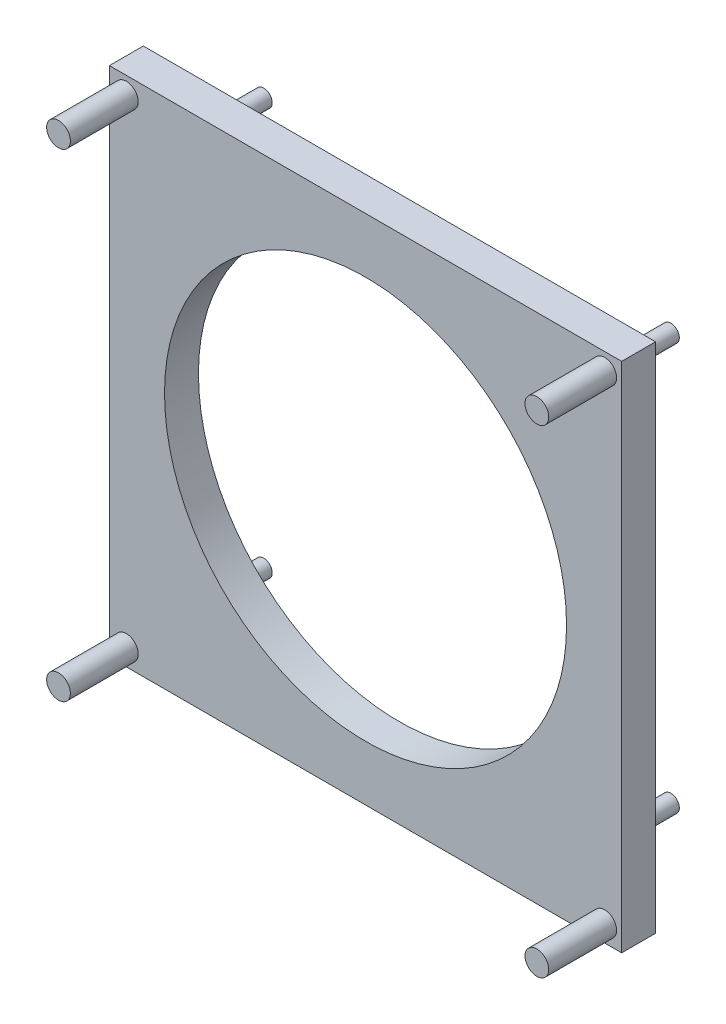
SolidWorks part; units mm, degrees
ref_plane "Front Plane" through (0, 0, 0) normal (0, 0, 1) x (1, 0, 0)
ref_plane "Top Plane" through (0, 0, 0) normal (0, 1, 0) x (1, 0, 0)
ref_plane "Right Plane" through (0, 0, 0) normal (1, 0, 0) x (0, 0, -1)
sketch "Sketch1" plane through (0, 0, 0) normal (0, 0, 1) x (1, 0, 0)
  line L1 (-225.7582, 128.2518) -> (-74.7582, 128.2518)
  line L2 (-225.7582, 128.2518) -> (-225.7582, -22.7482)
  line L3 (-225.7582, -22.7482) -> (-74.7582, -22.7482)
  line L4 (-74.7582, 128.2518) -> (-74.7582, -22.7482)
  line L5 (-225.7582, 128.2518) -> (-74.7582, -22.7482) construction
  line L6 (-225.7582, -22.7482) -> (-74.7582, 128.2518) construction
  point P0 (-150.2582, 52.7518)
  dimension "D1" = 151
  dimension "D2" = 151
extrude "Boss-Extrude1" add sketch "Sketch1" along normal blind 10
sketch "Sketch3" plane through (0, 0, 10) normal (0, 0, 1) x (1, 0, 0)
  line L0 (-150.2582, 128.2518) -> (-150.2582, -22.7482) construction
  line L1 (-74.7582, 128.2518) -> (-225.7582, 128.2518) construction
  line L2 (-225.7582, -22.7482) -> (-74.7582, -22.7482) construction
  line L3 (-74.7582, 52.7518) -> (-225.7582, 52.7518) construction
  line L4 (-74.7582, -22.7482) -> (-74.7582, 128.2518) construction
  line L5 (-225.7582, 128.2518) -> (-225.7582, -22.7482) construction
  circle A0 centre (-150.2582, 52.7518) radius 59.25
  dimension "D1" = 118.5
extrude "Cut-Extrude1" cut sketch "Sketch3" against normal through all
sketch "Sketch4" plane through (0, 0, 10) normal (0, 0, 1) x (1, 0, 0)
  line L0 (-220.7582, 128.2518) -> (-220.7582, -22.7482) construction
  line L1 (-74.7582, 128.2518) -> (-225.7582, 128.2518) construction
  line L2 (-225.7582, -22.7482) -> (-74.7582, -22.7482) construction
  line L3 (-225.7582, -17.7482) -> (-74.7582, -17.7482) construction
  line L4 (-225.7582, 128.2518) -> (-225.7582, -22.7482) construction
  line L5 (-74.7582, -22.7482) -> (-74.7582, 128.2518) construction
  line L6 (-79.7582, -22.7482) -> (-79.7582, 128.2518) construction
  line L7 (-225.7582, 123.2518) -> (-74.7582, 123.2518) construction
  circle A0 centre (-79.7582, -17.7482) radius 3.5
  circle A1 centre (-220.7582, -17.7482) radius 3.5
  circle A2 centre (-79.7582, 123.2518) radius 3.5
  circle A3 centre (-220.7582, 123.2518) radius 3.5
  dimension "D1" = 5
  dimension "D2" = 5
  dimension "D3" = 5
  dimension "D4" = 5
extrude "Boss-Extrude2" add sketch "Sketch4" along normal blind 20
sketch "Sketch5" plane through (0, 0, 0) normal (0, 0, -1) x (-1, 0, 0)
  line L0 (74.7582, -7.2482) -> (225.7582, -7.2482) construction
  line L1 (74.7582, -22.7482) -> (74.7582, 128.2518) construction
  line L2 (225.7582, 128.2518) -> (225.7582, -22.7482) construction
  line L3 (225.7582, -7.2482) -> (210.2582, -22.7482) construction
  line L4 (225.7582, -22.7482) -> (74.7582, -22.7482) construction
  line L5 (210.2582, -22.7482) -> (210.2582, 128.2518) construction
  line L6 (74.7582, 128.2518) -> (225.7582, 128.2518) construction
  line L7 (210.2582, 128.2518) -> (225.7582, 112.7518) construction
  line L8 (225.7582, 112.7518) -> (74.7582, 112.7518) construction
  line L9 (74.7582, 112.7518) -> (90.2582, 128.2518) construction
  line L10 (90.2582, 128.2518) -> (90.2582, -22.7482) construction
  line L11 (90.2582, -22.7482) -> (74.7582, -7.2482) construction
  circle A0 centre (90.2582, -7.2482) radius 2.5
  circle A1 centre (90.2582, 112.7518) radius 2.5
  circle A2 centre (210.2582, 112.7518) radius 2.5
  circle A3 centre (210.2582, -7.2482) radius 2.5
  dimension "D1" = 15.5
extrude "Boss-Extrude3" add sketch "Sketch5" along normal blind 20
equation "\"susan_side\"=151"
equation "\"D2@Sketch1\"=\"susan_side\""
equation "\"D1@Sketch1\"=\"susan_side\""
equation "\"susan_thickness\"=9.5"
equation "\"TXD1@Scheme2\"=\"susan_thickness\""
equation "\"s_hole_diam\"=118.5"
equation "\"D1@Sketch3\" = \"s_hole_diam\""
